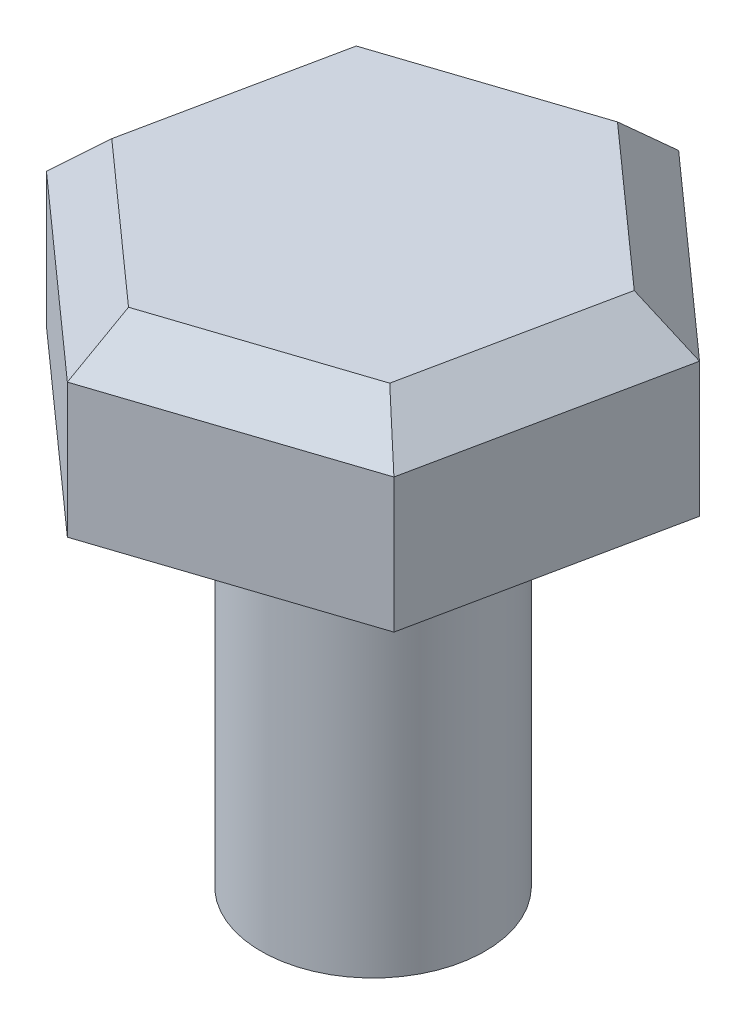
SolidWorks part; units mm, degrees
ref_plane "Front Plane" through (0, 0, 0) normal (0, 0, 1) x (1, 0, 0)
ref_plane "Top Plane" through (0, 0, 0) normal (0, 1, 0) x (1, 0, 0)
ref_plane "Right Plane" through (0, 0, 0) normal (1, 0, 0) x (0, 0, -1)
sketch "Sketch2" plane through (0, 0, 0) normal (0, 1, 0) x (1, 0, 0)
  line L1 (5.4822, 1.8108) -> (1.1729, 5.6531)
  line L2 (1.1729, 5.6531) -> (-4.3093, 3.8423)
  line L3 (-4.3093, 3.8423) -> (-5.4822, -1.8108)
  line L4 (-5.4822, -1.8108) -> (-1.1729, -5.6531)
  line L5 (-1.1729, -5.6531) -> (4.3093, -3.8423)
  line L6 (4.3093, -3.8423) -> (5.4822, 1.8108)
  circle A0 centre (0, 0) radius 5 construction
  dimension "D1" = 10
extrude "Boss-Extrude1" add sketch "Sketch2" along normal blind 4
chamfer "Chamfer2" distance 1 angle 45 6 edges at (1.5682, 4, 4.7477) (-3.3275, 4, 3.7319) (-4.8957, 4, -1.0158) (-1.5682, 4, -4.7477) (3.3275, 4, -3.7319) (4.8957, 4, 1.0158)
sketch "Sketch4" plane through (0, 0, 0) normal (0, -1, 0) x (1, 0, 0)
  circle A0 centre (0, 0) radius 2.5
extrude "Boss-Extrude3" add sketch "Sketch4" along normal blind 9
